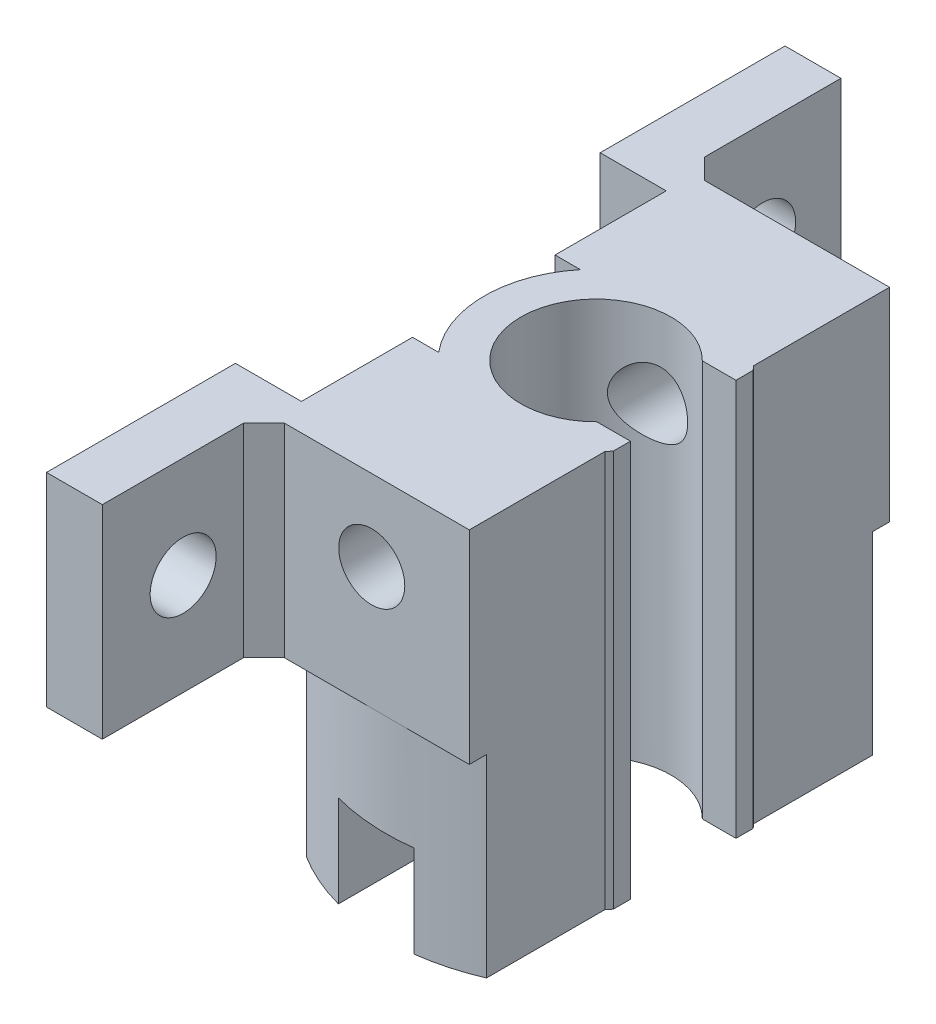
SolidWorks part; units mm, degrees
ref_plane "前基準面" through (0, 0, 0) normal (0, 0, 1) x (1, 0, 0)
ref_plane "上基準面" through (0, 0, 0) normal (0, 1, 0) x (1, 0, 0)
ref_plane "右基準面" through (0, 0, 0) normal (1, 0, 0) x (0, 0, -1)
sketch "草圖1" plane through (0, 0, 0) normal (0, 1, 0) x (1, 0, 0)
  circle A0 centre (0, 0) radius 9.68
  dimension "D1" = 19.36
extrude "伸長-薄件1" add sketch "草圖1" along normal blind 116.68 thin
ref_plane "平面1" through (-21, 0, 0) normal (1, 0, 0) x (0, 0, -1)
sketch "草圖11" plane through (0, 116.68, 0) normal (0, 1, 0) x (1, 0, 0)
  line L0 (-993.1634, -44.2358) -> (49006.8366, -44.2358) construction
  line L2 (35.2085, 30.7642) -> (8.2085, 30.7642)
  line L3 (35.2085, 30.7642) -> (35.2085, -119.2358)
  line L4 (35.2085, -119.2358) -> (8.2085, -119.2358)
  line L5 (8.2085, 30.7642) -> (8.2085, -119.2358)
  line L6 (35.2085, 30.7642) -> (8.2085, -119.2358) construction
  line L7 (35.2085, -119.2358) -> (8.2085, 30.7642) construction
  circle A0 centre (0, 0) radius 20.68 construction
  point P1 (21.7085, -44.2358)
  dimension "D1" = 150
  dimension "D2" = 27
  dimension "D3" = 30.7642
extrude "除料-伸長3" cut sketch "草圖11" against normal blind 40
ref_plane "平面2" through (0, 0, 21) normal (0, 0, 1) x (1, 0, 0)
sketch "草圖13" plane through (0, 0, 21) normal (0, 0, 1) x (1, 0, 0)
  line L0 (-21, -22.649) -> (-21, 22.649) construction
  line L1 (-21, 122.7847) -> (-11, 122.7847)
  line L2 (-21, 122.7847) -> (-21, -5.5603)
  line L3 (-21, -5.5603) -> (-11, -5.5603)
  line L4 (-11, 122.7847) -> (-11, -5.5603)
  dimension "D1" = 10
extrude "除料-伸長7" cut sketch "草圖13" against normal through all
sketch "草圖15" plane through (0, 0, 21) normal (0, 0, 1) x (1, 0, 0)
  line L0 (-1.3957, -883.32) -> (-1.3957, 49116.68) construction
  line L1 (8.2085, 116.68) -> (-11, 116.68) construction
  line L2 (-11, 0) -> (20.68, 0) construction
  line L3 (2.6043, 86.68) -> (-5.3957, 86.68)
  line L4 (2.6043, 86.68) -> (2.6043, 18)
  line L5 (2.6043, 18) -> (-5.3957, 18)
  line L6 (-5.3957, 86.68) -> (-5.3957, 18)
  line L7 (2.6043, 86.68) -> (-5.3957, 18) construction
  line L8 (2.6043, 18) -> (-5.3957, 86.68) construction
  point P1 (-1.3957, 52.34)
  point P5 (-1.3957, 116.68)
  dimension "D1" = 30
  dimension "D2" = 18
  dimension "D3" = 8
extrude "除料-伸長9" cut sketch "草圖15" against normal blind 48
sketch "草圖16" plane through (8.2085, 0, 0) normal (1, 0, 0) x (0, 0, -1)
  line L0 (20.68, 86.68) -> (20.68, 116.68) construction
  line L1 (5.1306, 116.68) -> (20.68, 116.68)
  line L2 (5.1306, 116.68) -> (5.1306, 96.68)
  line L3 (5.1306, 96.68) -> (20.68, 96.68)
  line L4 (20.68, 116.68) -> (20.68, 96.68)
  line L5 (-5.1306, 76.68) -> (-5.1306, 116.68) construction
  line L6 (-5.1306, 96.68) -> (-20.59, 96.68)
  line L7 (-5.1306, 96.68) -> (-5.1306, 116.68)
  line L8 (-5.1306, 116.68) -> (-20.59, 116.68)
  line L9 (-20.59, 96.68) -> (-20.59, 116.68)
  line L10 (-17.5118, 116.68) -> (-20.68, 116.68) construction
  dimension "D1" = 20
extrude "填料-伸長4" add sketch "草圖16" against normal blind 19.2
sketch "草圖17" plane through (0, 116.68, 0) normal (0, 1, 0) x (1, 0, 0)
  line L0 (-1009.59, 0) -> (48990.41, 0) construction
  line L1 (8.2085, 20.68) -> (8.2085, 5.1306) construction
  line L2 (8.2085, 6.97) -> (-11, 6.97)
  line L3 (8.2085, 6.97) -> (8.2085, -7.06)
  line L4 (8.2085, -7.06) -> (-11, -7.06)
  line L5 (-11, 6.97) -> (-11, -7.06)
  line L6 (-11, -17.5118) -> (-11, 17.5118) construction
  line L7 (-10.9915, -20.59) -> (-1.9273, -20.59) construction
  arc A0 (-8.2085, 5.1306) -> (-8.2085, -5.1306) centre (0, 0) ccw construction
  point P6 (-9.68, 0)
  dimension "D1" = 14.03
  dimension "D2" = 13.53
extrude "除料-伸長10" cut sketch "草圖17" against normal blind 20.2
sketch "草圖18" plane through (0, 0, 0) normal (0, -1, 0) x (1, 0, 0)
  circle A0 centre (0, 0) radius 9.59
extrude "除料-伸長11" cut sketch "草圖18" against normal through all
sketch "草圖21" plane through (0, 0, -20.68) normal (0, 0, -1) x (-1, 0, 0)
  line L0 (1.3915, 96.68) -> (1.3915, 105.73) construction
  line L1 (0, 96.68) -> (10.9915, 96.68) construction
  line L2 (1.3915, 105.73) -> (1.3915, 108.73) construction
  circle A0 centre (1.3915, 108.73) radius 2.985
  dimension "D3" = 5.97
  dimension "D1" = 9.05
  dimension "D2" = 3
extrude "除料-伸長12" cut sketch "草圖21" against normal blind 55.2
sketch "草圖23" plane through (0, 0, -20.68) normal (0, 0, -1) x (-1, 0, 0)
  line L0 (1.3915, 105.745) -> (1.3915, -11.785) construction
  circle A0 centre (1.3915, 108.73) radius 2.985 construction
  dimension "D1" = 117.53
sketch "草圖24" plane through (0, 0, 0) normal (0, -1, 0) x (1, 0, 0)
  circle A0 centre (0, 0) radius 9.59
extrude "伸長-薄件2" add sketch "草圖24" along normal blind 55.2 thin
sketch "草圖25" plane through (0, 0, 21) normal (0, 0, 1) x (1, 0, 0)
  line L0 (-1.3915, -11.785) -> (22.6124, -11.785)
  line L1 (22.6124, -11.785) -> (22.6124, -63.8733)
  line L2 (-22.7495, -63.8733) -> (22.6124, -63.8733)
  line L3 (-22.7495, -63.8733) -> (-22.7495, -11.785)
  line L4 (-22.7495, -11.785) -> (-1.3915, -11.785)
extrude "除料-伸長13" cut sketch "草圖25" against normal blind 55.2
sketch "草圖26" plane through (0, 0, 0) normal (0, 1, 0) x (1, 0, 0)
  line L0 (-21, -22.649) -> (-21, 22.649) construction
  line L1 (-10.9915, 20.68) -> (-21, 20.68)
  line L2 (-10.9915, 20.68) -> (-10.9915, -21)
  line L3 (-10.9915, -21) -> (-21, -21)
  line L4 (-21, 20.68) -> (-21, -21)
  line L5 (-17.6, -21) -> (17.6, -21) construction
extrude "除料-伸長15" cut sketch "草圖26" against normal blind 55.2
ref_plane "平面3" through (21, 0, 0) normal (1, 0, 0) x (0, 0, -1)
sketch "草圖27" plane through (21, 0, 0) normal (1, 0, 0) x (0, 0, -1)
  line L0 (0, -923.32) -> (0, 49076.68) construction
  line L1 (5.1306, 76.68) -> (-5.1306, 76.68) construction
  line L2 (18.9811, 76.68) -> (-18.9811, 76.68) construction
  line L3 (-5, 61.68) -> (5, 61.68)
  line L4 (-5, 61.68) -> (-5, 21.68)
  line L5 (-5, 21.68) -> (5, 21.68)
  line L6 (5, 61.68) -> (5, 21.68)
  line L7 (-5, 61.68) -> (5, 21.68) construction
  line L8 (-5, 21.68) -> (5, 61.68) construction
  point P1 (0, 41.68)
  point P5 (0, 76.68)
  dimension "D1" = 15
  dimension "D2" = 40
  dimension "D3" = 10
extrude "除料-伸長16" cut sketch "草圖27" against normal blind 55.2
sketch "草圖28" plane through (21, 0, 0) normal (1, 0, 0) x (0, 0, -1)
  line L1 (-22.4403, 4.804) -> (22.4403, 4.804)
  line L2 (-22.4403, 4.804) -> (-22.4403, -4.804)
  line L3 (-22.4403, -4.804) -> (22.4403, -4.804)
  line L4 (22.4403, 4.804) -> (22.4403, -4.804)
  line L5 (-22.4403, 4.804) -> (22.4403, -4.804) construction
  line L6 (-22.4403, -4.804) -> (22.4403, 4.804) construction
  point P0 (0, 0)
extrude "除料-伸長17" cut sketch "草圖28" against normal blind 12.2
sketch "草圖35" plane through (-10.9915, 0, 0) normal (-1, 0, 0) x (0, 0, 1)
  line L0 (20.59, 116.68) -> (20.59, 96.68)
  line L1 (20.59, 96.68) -> (7.06, 96.68)
  line L2 (7.06, 96.68) -> (7.06, 116.68)
  line L3 (7.06, 116.68) -> (20.59, 116.68)
extrude "填料-伸長10" add sketch "草圖35" along normal blind 15
sketch "草圖36" plane through (-10.9915, 0, 0) normal (-1, 0, 0) x (0, 0, 1)
  line L0 (-20.68, 116.68) -> (-6.97, 116.68)
  line L1 (-6.97, 116.68) -> (-6.97, 96.48)
  line L2 (-6.97, 96.48) -> (-20.68, 96.68)
  line L3 (-20.68, 96.68) -> (-20.68, 116.68)
extrude "填料-伸長11" add sketch "草圖36" along normal blind 15
sketch "草圖37" plane through (0, 0, 20.59) normal (0, 0, 1) x (1, 0, 0)
  line L0 (-25.9915, 96.68) -> (-1.9273, 96.68) construction
  line L1 (-25.9915, 116.68) -> (-16.9915, 116.68)
  line L2 (-25.9915, 116.68) -> (-25.9915, 96.68)
  line L3 (-25.9915, 96.68) -> (-16.9915, 96.68)
  line L4 (-16.9915, 116.68) -> (-16.9915, 96.68)
  dimension "D1" = 9
extrude "填料-伸長12" add sketch "草圖37" along normal blind 20
sketch "草圖38" plane through (0, 0, -20.68) normal (0, 0, -1) x (-1, 0, 0)
  line L0 (25.9915, 116.68) -> (-8.2085, 116.68) construction
  line L1 (25.9915, 96.68) -> (16.9915, 96.68)
  line L2 (25.9915, 96.68) -> (25.9915, 116.68)
  line L3 (25.9915, 116.68) -> (16.9915, 116.68)
  line L4 (16.9915, 96.68) -> (16.9915, 116.68)
  dimension "D1" = 9
extrude "填料-伸長13" add sketch "草圖38" along normal blind 20
sketch "草圖42" plane through (-16.9915, 0, 0) normal (1, 0, 0) x (0, 0, -1)
  line L0 (30.68, -903.32) -> (30.68, 49096.68) construction
  line L1 (40.68, 96.68) -> (20.68, 96.68) construction
  line L2 (-959.32, 106.68) -> (49040.68, 106.68) construction
  line L3 (40.68, 116.68) -> (40.68, 96.68) construction
  line L4 (-30.59, -903.32) -> (-30.59, 49096.68) construction
  line L5 (-40.59, 96.68) -> (-20.59, 96.68) construction
  circle A0 centre (30.68, 106.5544) radius 2.985
  circle A1 centre (-30.3956, 106.68) radius 2.985
  point P5 (30.68, 96.68)
  point P10 (40.68, 106.68)
  point P15 (-30.59, 96.68)
  dimension "D1" = 5.97
  dimension "D2" = 5.97
extrude "除料-伸長21" cut sketch "草圖42" against normal blind 20
sketch "草圖43" plane through (0, 116.68, 0) normal (0, 1, 0) x (1, 0, 0)
  line L0 (-11, 6.97) -> (-10.9915, 20.68)
  line L1 (-10.9915, 20.68) -> (-10.9915, 48.0968)
  line L2 (-10.9915, 48.0968) -> (-28.2748, 48.0968)
  line L3 (-28.2748, 48.0968) -> (-28.2748, -43.2705)
  line L4 (-28.2748, -43.2705) -> (-11, -43.2705)
  line L5 (-11, -43.2705) -> (-11, 6.97)
extrude "除料-伸長23" cut sketch "草圖43" against normal through all
sketch "草圖45" plane through (0, 0, 20.59) normal (0, 0, 1) x (1, 0, 0)
  line L0 (-11, 96.68) -> (-1.9273, 96.68) construction
  line L1 (-11, 116.68) -> (-8, 116.68)
  line L2 (-11, 116.68) -> (-11, 96.68)
  line L3 (-11, 96.68) -> (-8, 96.68)
  line L4 (-8, 116.68) -> (-8, 96.68)
  dimension "D1" = 3
extrude "填料-伸長14" add sketch "草圖45" along normal blind 30
sketch "草圖46" plane through (0, 0, -20.68) normal (0, 0, -1) x (-1, 0, 0)
  line L0 (0, 96.68) -> (10.9915, 96.68) construction
  line L1 (10.9915, 116.68) -> (7.9915, 116.68)
  line L2 (10.9915, 116.68) -> (10.9915, 96.68)
  line L3 (10.9915, 96.68) -> (7.9915, 96.68)
  line L4 (7.9915, 116.68) -> (7.9915, 96.68)
  dimension "D1" = 3
extrude "填料-伸長15" add sketch "草圖46" along normal blind 30
sketch "草圖47" plane through (-11, 0, 0) normal (-1, 0, 0) x (0, 0, 1)
  line L0 (50.59, 116.68) -> (7.06, 116.68) construction
  line L1 (50.59, 96.68) -> (17.5118, 96.68)
  line L2 (50.59, 96.68) -> (50.59, 116.68)
  line L3 (50.59, 116.68) -> (17.5118, 116.68)
  line L4 (17.5118, 96.68) -> (17.5118, 116.68)
extrude "填料-伸長16" add sketch "草圖47" along normal blind 50
sketch "草圖48" plane through (-10.9915, 0, 0) normal (-1, 0, 0) x (0, 0, 1)
  line L1 (-50.68, 116.68) -> (-20.68, 116.68)
  line L2 (-50.68, 116.68) -> (-50.68, 96.68)
  line L3 (-50.68, 96.68) -> (-20.68, 96.68)
  line L4 (-20.68, 116.68) -> (-20.68, 96.68)
extrude "填料-伸長17" add sketch "草圖48" along normal blind 50
sketch "草圖50" plane through (0, 0, 17.5118) normal (0, 0, -1) x (-1, 0, 0)
  line L0 (11, 96.68) -> (11, 116.68)
  line L1 (11, 116.68) -> (61, 116.68)
  line L2 (61, 116.68) -> (61, 96.68)
  line L3 (61, 96.68) -> (11, 96.68)
extrude "填料-伸長18" add sketch "草圖50" along normal blind 1
sketch "草圖51" plane through (0, 0, -20.68) normal (0, 0, 1) x (1, 0, 0)
  line L0 (-10.9915, 116.68) -> (-10.9915, 96.68)
  line L1 (-10.9915, 96.68) -> (-60.9915, 96.68)
  line L2 (-60.9915, 96.68) -> (-60.9915, 116.68)
  line L3 (-60.9915, 116.68) -> (-10.9915, 116.68)
extrude "填料-伸長19" add sketch "草圖51" along normal blind 1
sketch "草圖52" plane through (0, 116.68, 0) normal (0, 1, 0) x (1, 0, 0)
  line L0 (-34.4915, -949.32) -> (-34.4915, 49050.68) construction
  line L1 (-60.9915, 50.68) -> (-7.9915, 50.68) construction
  line L2 (-1007.9915, 35.68) -> (48992.0085, 35.68) construction
  line L3 (-7.9915, 50.68) -> (-7.9915, 20.68) construction
  line L4 (-60.9915, 19.68) -> (-60.9915, 50.68) construction
  line L5 (-7.9915, 50.68) -> (-60.9915, 50.68)
  line L6 (-7.9915, 50.68) -> (-7.9915, 36.68)
  line L7 (-7.9915, 36.68) -> (-60.9915, 36.68)
  line L8 (-60.9915, 50.68) -> (-60.9915, 36.68)
  point P5 (-34.4915, 50.68)
  point P10 (-7.9915, 35.68)
  dimension "D1" = 14
extrude "除料-伸長24" cut sketch "草圖52" against normal through all
sketch "草圖53" plane through (0, 116.68, 0) normal (0, 1, 0) x (1, 0, 0)
  line L0 (-61, -50.59) -> (-61, -16.5118) construction
  line L1 (-8, -50.59) -> (-61, -50.59)
  line L2 (-8, -50.59) -> (-8, -36.59)
  line L3 (-8, -36.59) -> (-61, -36.59)
  line L4 (-61, -50.59) -> (-61, -36.59)
  dimension "D1" = 14
extrude "除料-伸長25" cut sketch "草圖53" against normal through all
sketch "草圖54" plane through (0, 116.68, 0) normal (0, 1, 0) x (1, 0, 0)
  line L0 (-60.9915, 36.68) -> (-7.9915, 36.68) construction
  line L1 (-61, -36.59) -> (-21, -36.59)
  line L2 (-61, -36.59) -> (-61, 36.68)
  line L3 (-61, 36.68) -> (-21, 36.68)
  line L4 (-21, -36.59) -> (-21, 36.68)
  dimension "D1" = 40
extrude "除料-伸長26" cut sketch "草圖54" against normal through all
sketch "草圖55" plane through (0, 116.68, 0) normal (0, 1, 0) x (1, 0, 0)
  line L0 (-15.0276, -36.59) -> (-15.0276, -16.5118) construction
  line L1 (-8, -36.59) -> (-21, -36.59) construction
  line L2 (-21, -16.5118) -> (-11, -16.5118) construction
  line L3 (-13.4574, 19.68) -> (-13.4574, 39.76) construction
  line L4 (-10.9921, 19.68) -> (-21, 19.68) construction
  dimension "D1" = 20.08
sketch "草圖56" plane through (0, 0, -36.68) normal (0, 0, -1) x (-1, 0, 0)
  line L1 (7.9915, 96.68) -> (21, 96.68)
  line L2 (7.9915, 96.68) -> (7.9915, 116.68)
  line L3 (7.9915, 116.68) -> (21, 116.68)
  line L4 (21, 96.68) -> (21, 116.68)
extrude "填料-伸長21" add sketch "草圖56" along normal blind 3.08
ref_plane "平面4" through (0, 0, 50) normal (0, 0, 1) x (1, 0, 0)
sketch "草圖58" plane through (0, 0, 50) normal (0, 0, 1) x (1, 0, 0)
  line L1 (-22.571, -18.3082) -> (22.1011, -18.3082)
  line L2 (-22.571, -18.3082) -> (-22.571, 77.6317)
  line L3 (-22.571, 77.6317) -> (22.1011, 77.6317)
  line L4 (22.1011, -18.3082) -> (22.1011, 77.6317)
extrude "除料-伸長28" cut sketch "草圖58" against normal through all
sketch "草圖59" plane through (0, 77.6317, 0) normal (0, -1, 0) x (1, 0, 0)
  circle A0 centre (0, 0) radius 9.7
  dimension "D1" = 19.4
extrude "除料-伸長29" cut sketch "草圖59" against normal through all
sketch "草圖60" plane through (0, 116.68, 0) normal (0, 1, 0) x (1, 0, 0)
  line L0 (-21, 39.76) -> (-7.9915, 39.76) construction
  line L1 (-21, -36.59) -> (-14.4957, -36.59)
  line L2 (-21, -36.59) -> (-21, 39.76)
  line L3 (-21, 39.76) -> (-14.4957, 39.76)
  line L4 (-14.4957, -36.59) -> (-14.4957, 39.76)
extrude "除料-伸長30" cut sketch "草圖60" against normal through all
sketch "草圖61" plane through (0, 116.68, 0) normal (0, 1, 0) x (1, 0, 0)
  line L0 (1.9273, -20.59) -> (1.9273, -22.3991)
  line L1 (1.9273, -22.3991) -> (-2.1742, -21.4215)
  line L2 (-2.1742, -21.4215) -> (-2.1742, -20.59)
  line L3 (-8, -20.59) -> (-1.9273, -20.59) construction
  line L4 (-2.1742, -20.59) -> (1.9273, -20.59)
extrude "除料-伸長32" cut sketch "草圖61" against normal blind 20
sketch "草圖64" plane through (0, 116.68, 0) normal (0, 1, 0) x (1, 0, 0)
  line L1 (-8, -20.59) -> (8.2085, -20.59)
  line L2 (-8, -20.59) -> (-8, -20.68)
  line L3 (-8, -20.68) -> (8.2085, -20.68)
  line L4 (8.2085, -20.59) -> (8.2085, -20.68)
  dimension "D1" = 0.09
extrude "填料-伸長22" add sketch "草圖64" against normal blind 20
sketch "草圖65" plane through (0, 116.68, 0) normal (0, 1, 0) x (1, 0, 0)
  line L0 (-11, 6.97) -> (-10.9921, 19.68) construction
  line L1 (-11, -7.06) -> (-11, -16.5118) construction
  line L2 (-14.4957, -36.59) -> (-14.4957, -16.5118) construction
  line L3 (-11, -16.5118) -> (-14.4957, -16.5118)
  line L4 (-11, -16.5118) -> (-11, -19.7718)
  line L5 (-11, -19.7718) -> (-14.4957, -19.7718)
  line L6 (-14.4957, -16.5118) -> (-14.4957, -19.7718)
  dimension "D1" = 12.71
  dimension "D2" = 9.4518
  dimension "D3" = 3.26
extrude "除料-伸長33" cut sketch "草圖65" against normal through all
sketch "草圖66" plane through (0, 96.48, 0) normal (0, 1, 0) x (1, 0, 0)
  line L0 (-1011, -0.045) -> (48989, -0.045) construction
  line L1 (-11, 6.97) -> (-11, -7.06) construction
  line L2 (-12.9194, -0.045) -> (-12.9194, 17.905) construction
  line L3 (-12.9194, -0.045) -> (-12.9194, -17.995) construction
  line L4 (-11, -19.7718) -> (-11, -7.06) construction
  line L5 (-14.4957, -19.7718) -> (-11, -19.7718)
  line L6 (-14.4957, -19.7718) -> (-14.4957, -17.995)
  line L7 (-14.4957, -17.995) -> (-11, -17.995)
  line L8 (-11, -19.7718) -> (-11, -17.995)
  line L10 (-10.9921, 19.68) -> (-14.4957, 19.68)
  line L11 (-10.9921, 19.68) -> (-10.9921, 17.905)
  line L12 (-10.9921, 17.905) -> (-14.4957, 17.905)
  line L13 (-14.4957, 19.68) -> (-14.4957, 17.905)
  point P5 (-11, -0.045)
  dimension "D1" = 17.95
  dimension "D2" = 17.95
extrude "填料-伸長23" add sketch "草圖66" along normal blind 20.2
sketch "草圖68" plane through (0, 116.68, 0) normal (0, 1, 0) x (1, 0, 0)
  line L0 (-10.9932, 17.905) -> (-10.9932, 39.76) construction
  line L1 (-14.4957, 39.76) -> (-7.9915, 39.76) construction
  line L2 (-14.4957, 17.905) -> (-14.4957, 39.76) construction
  line L3 (-7.9915, 39.76) -> (-14.4957, 39.76)
  line L4 (-7.9915, 39.76) -> (-7.9915, 36.1)
  line L5 (-7.9915, 36.1) -> (-14.4957, 36.1)
  line L6 (-14.4957, 39.76) -> (-14.4957, 36.1)
  dimension "D1" = 3.66
extrude "除料-伸長34" cut sketch "草圖68" against normal blind 20
sketch "草圖69" plane through (-7.9915, 0, 0) normal (1, 0, 0) x (0, 0, -1)
  line L0 (28.39, -903.32) -> (28.39, 49096.68) construction
  line L1 (36.1, 96.68) -> (20.68, 96.68) construction
  line L2 (-28.635, -903.32) -> (-28.635, 49096.68) construction
  line L3 (-36.59, 96.68) -> (-20.68, 96.68) construction
  line L4 (-963.9, 106.68) -> (49036.1, 106.68) construction
  line L5 (36.1, 96.68) -> (36.1, 116.68) construction
  circle A0 centre (28.39, 106.68) radius 2.985
  circle A1 centre (-28.635, 106.68) radius 2.985
  point P5 (28.39, 96.68)
  point P10 (-28.635, 96.68)
  point P15 (36.1, 106.68)
  dimension "D1" = 5.97
  dimension "D2" = 5.97
extrude "除料-伸長35" cut sketch "草圖69" against normal through all
sketch "草圖70" plane through (0, 0, 20.59) normal (0, 0, -1) x (-1, 0, 0)
  circle A0 centre (1.3915, 108.73) radius 2.985
  dimension "D1" = 5.97
extrude "除料-伸長36" cut sketch "草圖70" against normal through all
sketch "草圖71" plane through (-14.4957, 0, 0) normal (-1, 0, 0) x (0, 0, 1)
  line L1 (36.59, 96.68) -> (17.995, 96.68)
  line L2 (36.59, 96.68) -> (36.59, 116.68)
  line L3 (36.59, 116.68) -> (17.995, 116.68)
  line L4 (17.995, 96.68) -> (17.995, 116.68)
  line L5 (-36.1, 116.68) -> (-17.905, 116.68)
  line L6 (-36.1, 116.68) -> (-36.1, 96.6395)
  line L7 (-36.1, 96.6395) -> (-17.905, 96.6395)
  line L8 (-17.905, 116.68) -> (-17.905, 96.6395)
extrude "填料-伸長24" add sketch "草圖71" along normal blind 10
sketch "草圖72" plane through (-8, 0, 0) normal (1, 0, 0) x (0, 0, -1)
  circle A0 centre (-28.635, 106.68) radius 3.05
  circle A1 centre (28.39, 106.68) radius 3.05
  dimension "D1" = 6.1
  dimension "D2" = 6.1
extrude "除料-伸長37" cut sketch "草圖72" against normal through all
sketch "草圖73" plane through (0, 116.68, 0) normal (0, 1, 0) x (1, 0, 0)
  line L1 (-7.9915, 36.1) -> (-11.9915, 36.1)
  line L2 (-7.9915, 36.1) -> (-7.9915, 20.68)
  line L3 (-7.9915, 20.68) -> (-11.9915, 20.68)
  line L4 (-11.9915, 36.1) -> (-11.9915, 20.68)
  dimension "D1" = 4
extrude "除料-伸長39" cut sketch "草圖73" against normal through all
sketch "草圖74" plane through (0, 116.68, 0) normal (0, 1, 0) x (1, 0, 0)
  line L1 (-8, -36.59) -> (-12, -36.59)
  line L2 (-8, -36.59) -> (-8, -20.68)
  line L3 (-8, -20.68) -> (-12, -20.68)
  line L4 (-12, -36.59) -> (-12, -20.68)
  dimension "D1" = 4
extrude "除料-伸長40" cut sketch "草圖74" against normal through all
sketch "草圖75" plane through (0, 116.68, 0) normal (0, 1, 0) x (1, 0, 0)
  line L0 (-12, -20.68) -> (-12, -22.68)
  line L1 (-12, -20.68) -> (-12, -36.59) construction
  line L2 (-12, -22.68) -> (-10, -20.68)
  line L3 (-12, -20.68) -> (8.2085, -20.68) construction
  line L4 (-10, -20.68) -> (-12, -20.68)
  line L5 (-11.9915, 20.68) -> (-11.9915, 22.68)
  line L6 (-11.9915, 36.1) -> (-11.9915, 20.68) construction
  line L7 (-11.9915, 22.68) -> (-9.9915, 20.68)
  line L8 (-11.9915, 20.68) -> (8.2085, 20.68) construction
  line L9 (-9.9915, 20.68) -> (-11.9915, 20.68)
  dimension "D1" = 2
  dimension "D2" = 2
  dimension "D3" = 2
  dimension "D4" = 2
  dimension "D5" = 2.8284
extrude "填料-伸長25" add sketch "草圖75" against normal blind 20
sketch "草圖77" plane through (0, 116.68, 0) normal (0, 1, 0) x (1, 0, 0)
  line L0 (-12, -36.59) -> (-24.4957, -36.59) construction
  line L1 (-24.4957, 36.1) -> (-17.4957, 36.1)
  line L2 (-24.4957, 36.1) -> (-24.4957, -36.59)
  line L3 (-24.4957, -36.59) -> (-17.4957, -36.59)
  line L4 (-17.4957, 36.1) -> (-17.4957, -36.59)
  dimension "D1" = 7
extrude "除料-伸長41" cut sketch "草圖77" against normal through all
sketch "草圖78" plane through (0, 0, 50) normal (0, 0, 1) x (1, 0, 0)
  circle A0 centre (-1.3915, 108.73) radius 3.25
  dimension "D1" = 6.5
extrude "除料-伸長42" cut sketch "草圖78" against normal through all
sketch "草圖79" plane through (-11.9915, 0, 0) normal (1, 0, 0) x (0, 0, -1)
  circle A0 centre (28.39, 106.68) radius 3.25
  circle A1 centre (-28.635, 106.68) radius 3.25
  dimension "D1" = 6.5
  dimension "D2" = 6.5
extrude "除料-伸長43" cut sketch "草圖79" against normal blind 10 and the other way blind 10
sketch "草圖80" plane through (0, 116.68, 0) normal (0, 1, 0) x (1, 0, 0)
  circle A0 centre (0, 0) radius 6.995
  dimension "D1" = 13.99
extrude "伸長-薄件3" add sketch "草圖80" against normal blind 40 thin
sketch "草圖81" plane through (0, 0, 50) normal (0, 0, 1) x (1, 0, 0)
  line L0 (8.2085, 77.6317) -> (-11, 77.6317)
  line L1 (-11, 77.6317) -> (-10.995, 76.68)
  line L2 (-10.995, 76.68) -> (10.995, 76.68)
  line L3 (10.995, 76.68) -> (10.995, 77.6317)
  line L4 (10.995, 77.6317) -> (8.2085, 77.6317)
extrude "除料-伸長44" cut sketch "草圖81" against normal through all
sketch "草圖82" plane through (0, 116.68, 0) normal (0, 1, 0) x (1, 0, 0)
  line L1 (12.7421, 5.195) -> (1.2479, 5.195)
  line L2 (12.7421, 5.195) -> (12.7421, -5.195)
  line L3 (12.7421, -5.195) -> (1.2479, -5.195)
  line L4 (1.2479, 5.195) -> (1.2479, -5.195)
  line L5 (12.7421, 5.195) -> (1.2479, -5.195) construction
  line L6 (12.7421, -5.195) -> (1.2479, 5.195) construction
  circle A0 centre (0, 0) radius 6.995 construction
  point P0 (6.995, 0)
  dimension "D1" = 10.39
extrude "除料-伸長45" cut sketch "草圖82" against normal blind 43
sketch "草圖83" plane through (0, 0, 50) normal (0, 0, 1) x (1, 0, 0)
  circle A0 centre (-1.3915, 108.73) radius 3.25
extrude "除料-伸長46" cut sketch "草圖83" against normal blind 78
sketch "草圖84" plane through (0, 116.68, 0) normal (0, 1, 0) x (1, 0, 0)
  line L1 (12.6901, 8.2404) -> (8.5811, 8.2404)
  line L2 (12.6901, 8.2404) -> (12.6901, -8.6639)
  line L3 (12.6901, -8.6639) -> (8.5811, -8.6639)
  line L4 (8.5811, 8.2404) -> (8.5811, -8.6639)
extrude "除料-伸長47" cut sketch "草圖84" against normal blind 46
sketch "草圖85" plane through (0, 116.68, 0) normal (0, 1, 0) x (1, 0, 0)
  circle A0 centre (0, 0) radius 7.4
  dimension "D1" = 14.8
extrude "除料-伸長48" cut sketch "草圖85" against normal through all
